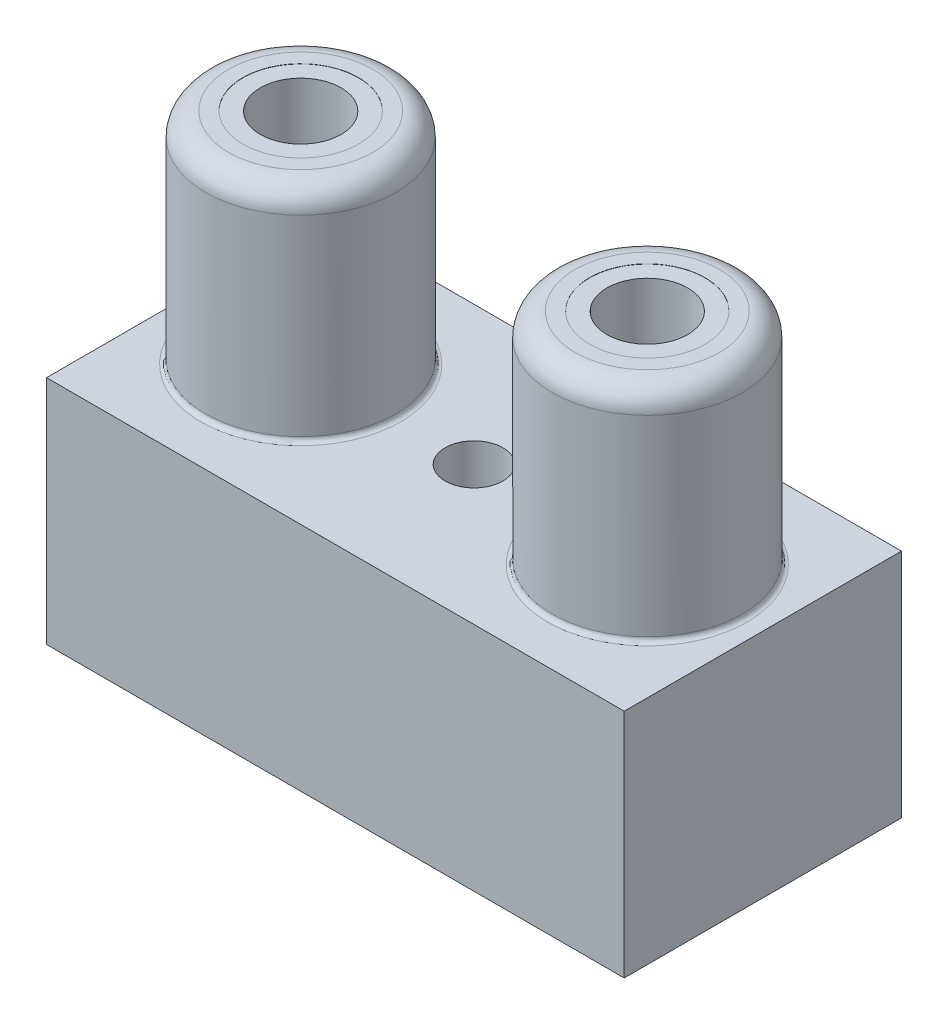
SolidWorks part; units mm, degrees
ref_plane "Plan de face" through (0, 0, 0) normal (0, 0, 1) x (1, 0, 0)
ref_plane "Plan de dessus" through (0, 0, 0) normal (0, 1, 0) x (1, 0, 0)
ref_plane "Plan de droite" through (0, 0, 0) normal (1, 0, 0) x (0, 0, -1)
sketch "Esquisse1" plane through (0, 0, 0) normal (0, 1, 0) x (1, 0, 0)
  line L1 (0, 0) -> (25, 0)
  line L2 (0, 0) -> (0, 12)
  line L3 (0, 12) -> (25, 12)
  line L4 (25, 0) -> (25, 12)
  dimension "D1" = 25
  dimension "D2" = 12
extrude "Boss.-Extru.1" add sketch "Esquisse1" along normal blind 10
sketch "Esquisse2" plane through (0, 10, 0) normal (0, 1, 0) x (1, 0, 0)
  line L0 (0, 12) -> (25, 0) construction
  line L1 (25, 0) -> (25, 12) construction
  line L2 (12.5, 6) -> (29.9533, 6) construction
  circle A0 centre (5, 6) radius 4.12
  circle A1 centre (20, 6) radius 4.12
  dimension "D1" = 8.24
  dimension "D2" = 8.24
  dimension "D3" = 15
  dimension "D4" = 7.5
extrude "Boss.-Extru.2" add sketch "Esquisse2" along normal blind 9.5
sketch "Esquisse3" plane through (0, 19.5, 0) normal (0, 1, 0) x (1, 0, 0)
  circle A0 centre (5, 6) radius 2.5
  circle A1 centre (20, 6) radius 2.5
  circle A2 centre (5, 6) radius 4.12 construction
  circle A3 centre (20, 6) radius 4.12 construction
  dimension "D1" = 5
  dimension "D2" = 5
extrude "Enlèv. mat.-Extru.1" cut sketch "Esquisse3" against normal blind 0.01
sketch "Esquisse4" plane through (0, 19.49, 0) normal (0, 1, 0) x (1, 0, 0)
  circle A0 centre (5, 6) radius 1.75
  circle A1 centre (20, 6) radius 1.75
  dimension "D1" = 3.5
  dimension "D2" = 3.5
extrude "Enlèv. mat.-Extru.2" cut sketch "Esquisse4" against normal blind 15
sketch "Esquisse5" plane through (0, 10, 0) normal (0, 1, 0) x (1, 0, 0)
  line L0 (0, 12) -> (25, 0) construction
  circle A0 centre (12.5, 6) radius 1.25
  dimension "D1" = 2.5
extrude "Enlèv. mat.-Extru.3" cut sketch "Esquisse5" against normal through all
fillet "Congé1" radius 1 2 edges at (20, 19.5, -1.88) (5, 19.5, -1.88)
fillet "Congé2" radius 0.2 2 edges at (20, 10, -10.12) (5, 10, -10.12)
